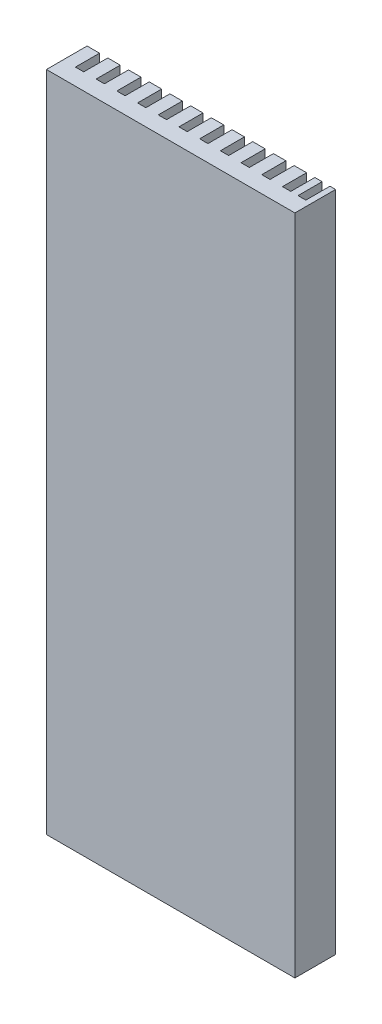
SolidWorks part; units mm, degrees
ref_plane "Спереди" through (0, 0, 0) normal (0, 0, 1) x (1, 0, 0)
ref_plane "Сверху" through (0, 0, 0) normal (0, 1, 0) x (1, 0, 0)
ref_plane "Справа" through (0, 0, 0) normal (1, 0, 0) x (0, 0, -1)
sketch "Эскиз1" plane through (0, 0, 0) normal (0, 1, 0) x (1, 0, 0)
  line L0 (-30, 0) -> (30, 0)
  line L1 (-30, 0) -> (-30, 9.8193)
  line L2 (30, 0) -> (30, 9.8193)
  line L3 (-30, 9.8193) -> (-27, 9.8193)
  line L4 (-27, 9.8193) -> (-27, 4)
  line L5 (-27, 4) -> (-25, 4)
  line L6 (-25, 4) -> (-25, 9.8193)
  line L7 (-22, 9.8193) -> (-22, 4)
  line L8 (-22, 4) -> (-20, 4)
  line L9 (-20, 4) -> (-20, 9.8193)
  line L10 (-25, 9.8193) -> (-22, 9.8193)
  line L11 (-17, 9.8193) -> (-17, 4)
  line L12 (-17, 4) -> (-15, 4)
  line L13 (-15, 4) -> (-15, 9.8193)
  line L14 (-20, 9.8193) -> (-17, 9.8193)
  line L15 (-12, 9.8193) -> (-12, 4)
  line L16 (-12, 4) -> (-10, 4)
  line L17 (-10, 4) -> (-10, 9.8193)
  line L18 (-15, 9.8193) -> (-12, 9.8193)
  line L19 (-7, 9.8193) -> (-7, 4)
  line L20 (-7, 4) -> (-5, 4)
  line L21 (-5, 4) -> (-5, 9.8193)
  line L22 (-10, 9.8193) -> (-7, 9.8193)
  line L23 (-2, 9.8193) -> (-2, 4)
  line L24 (-2, 4) -> (0, 4)
  line L25 (0, 4) -> (0, 9.8193)
  line L26 (-5, 9.8193) -> (-2, 9.8193)
  line L27 (3, 9.8193) -> (3, 4)
  line L28 (3, 4) -> (5, 4)
  line L29 (5, 4) -> (5, 9.8193)
  line L30 (0, 9.8193) -> (3, 9.8193)
  line L31 (8, 9.8193) -> (8, 4)
  line L32 (8, 4) -> (10, 4)
  line L33 (10, 4) -> (10, 9.8193)
  line L34 (5, 9.8193) -> (8, 9.8193)
  line L35 (13, 9.8193) -> (13, 4)
  line L36 (13, 4) -> (15, 4)
  line L37 (15, 4) -> (15, 9.8193)
  line L38 (10, 9.8193) -> (13, 9.8193)
  line L39 (18, 9.8193) -> (18, 4)
  line L40 (18, 4) -> (20, 4)
  line L41 (20, 4) -> (20, 9.8193)
  line L42 (15, 9.8193) -> (18, 9.8193)
  line L43 (23, 9.8193) -> (23, 4)
  line L44 (23, 4) -> (25, 4)
  line L45 (25, 4) -> (25, 9.8193)
  line L46 (20, 9.8193) -> (23, 9.8193)
  line L47 (25, 9.8193) -> (26.7474, 9.8193)
  line L48 (26.7474, 9.8193) -> (26.7474, 4)
  line L49 (26.7474, 4) -> (28.6446, 4)
  line L50 (28.6446, 4) -> (28.6446, 9.8193)
  line L51 (28.6446, 9.8193) -> (30, 9.8193)
  dimension "D1" = 11
extrude "Бобышка-Вытянуть1" add sketch "Эскиз1" along normal blind 160
